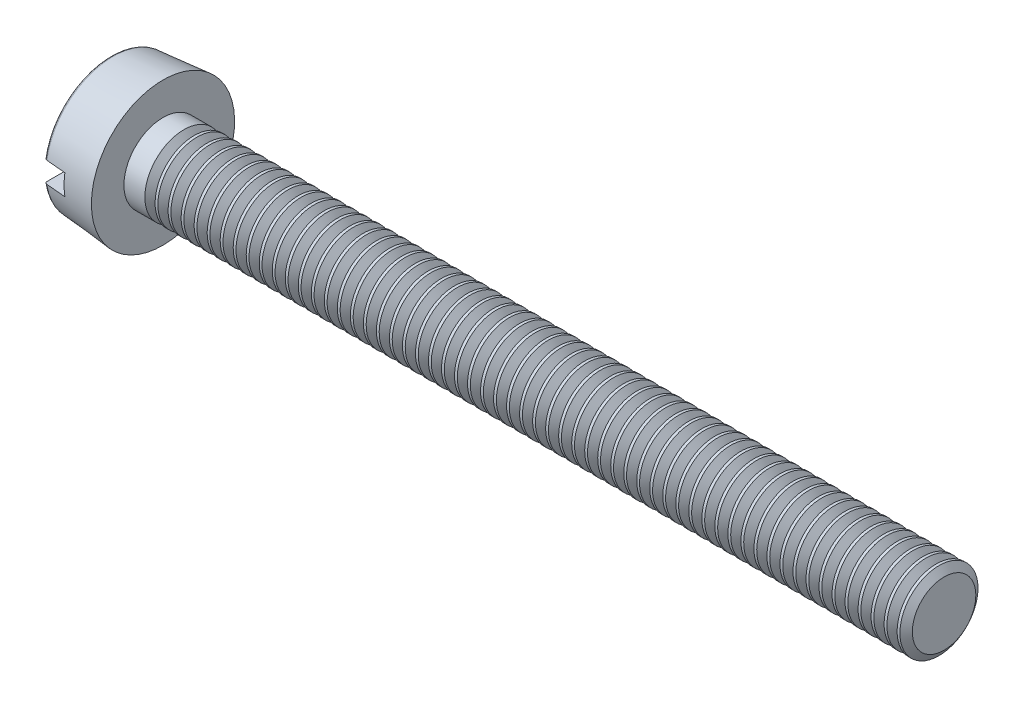
SolidWorks part; units mm, degrees
ref_plane "Plane1" through (0, 0, 0) normal (0, 0, 1) x (1, 0, 0)
ref_plane "Plane2" through (0, 0, 0) normal (0, 1, 0) x (1, 0, 0)
ref_plane "Plane3" through (0, 0, 0) normal (1, 0, 0) x (0, 0, -1)
sketch "BodySke" plane through (0, 0, 0) normal (0, 0, 1) x (1, 0, 0)
  line L0 (2, 1.5) -> (2, 2.75)
  line L1 (0, 0) -> (0, 2.575)
  line L2 (-25.4, 0) -> (127, 0) construction
  line L3 (32, 0) -> (0, 0)
  line L4 (2, 1.5) -> (32, 1.5)
  line L5 (32, 1.5) -> (32, 0)
  line L6 (0, 2.575) -> (2, 2.75)
  line L9 (2.5, 3.0875) -> (2.5, -6.4375) construction
  line L10 (2, 6.35) -> (2, -3.175) construction
  dimension "Length" = 30
  dimension "Head_ht" = 2
  dimension "Advance" = 0.5
  dimension "Thread_nom" = 30
  dimension "Head_dia" = 5.5
  dimension "Head_side_angle" = 5
  dimension "Diameter" = 3
revolve "Base-Revolve" add sketch "BodySke"
cosmetic thread "ThreadCosmetic" [suppressed]
fillet "Fillet1" [suppressed] radius 0.1
fillet "Fillet2" radius 0.1 1 edges at (0, 0, 2.575)
sketch "Sketch2" plane through (0, 0, 0) normal (1, 0, 0) x (0, 0, -1)
  line L0 (2.75, -0.4) -> (-2.75, -0.4)
  line L1 (2.75, -0.4) -> (2.75, 0.4)
  line L2 (-2.75, 0.4) -> (2.75, 0.4)
  line L3 (-2.75, 0.4) -> (-2.75, -0.4)
  dimension "D1" = 5.5
  dimension "Slot_width" = 0.8
  dimension "D2" = 2.75
  dimension "D3" = 0.4
extrude "Slot" cut sketch "Sketch2" along normal blind 0.85
sketch "ThdSchSke" plane through (0, 0, 0) normal (0, 0, 1) x (1, 0, 0)
  line L0 (3, -1.2195) -> (2.8036, -1.5)
  line L1 (3, -1.2195) -> (3.1964, -1.5)
  line L2 (3.1964, -1.5) -> (3.1964, -1.875)
  line L3 (-3.175, 0) -> (5.1513, 0) construction
  line L5 (3.1964, -1.875) -> (2.8036, -1.875)
  line L6 (2.8036, -1.875) -> (2.8036, -1.5)
  dimension "Diameter" = 3
  dimension "SideAngle" = 55
  dimension "VeeAngle" = 70
  dimension "Thread_minor" = 2.439
  dimension "Overcut" = 3.75
  dimension "Start" = 3
revolve "ThreadSchematic" cut sketch "ThdSchSke" angle 360 about L3
pattern_linear "ThdSchPat" count 59 spacing 0.5 along (1, 0, 0) of "ThreadSchematic"
equation "\"D1@Sketch2\" = \"Head_dia@BodySke\""
equation "\"D2@Sketch2\" = \"D1@Sketch2\" / 2"
equation "\"D3@Sketch2\" = \"Slot_width@Sketch2\" / 2"
equation "\"Thread_length@ThreadCosmetic\" = ((sgn( (\"Length@BodySke\" - \"Advance@BodySke\" * 2.0 ) - \"Thread_nom@BodySke\" )-1)*( (\"Length@BodySke\" - \"Advance@BodySke\"  * 2.0) - \"Thread_nom@BodySke\" ))/-2+ \"Thread_nom@BodySke\""
equation "\"Thread_minor@ThdSchSke\" = \"Thread_minor@ThreadCosmetic\""
equation "\"Diameter@ThdSchSke\" = \"Diameter@BodySke\""
equation "\"Overcut@ThdSchSke\" = \"Diameter@BodySke\" * 1.25"
equation "\"Start@ThdSchSke\" = \"Head_ht@BodySke\" + \"Length@BodySke\" - \"Thread_length@ThreadCosmetic\"  '---Non-countersunk---"
equation "\"Num_threads@ThdSchPat\" = int( \"Thread_length@ThreadCosmetic\" / \"Advance@BodySke\" + 0.999 )  + 1"
equation "\"Advance@ThdSchPat\" = \"Thread_length@ThreadCosmetic\" /  (\"Num_threads@ThdSchPat\" - 1) 'relax it"
